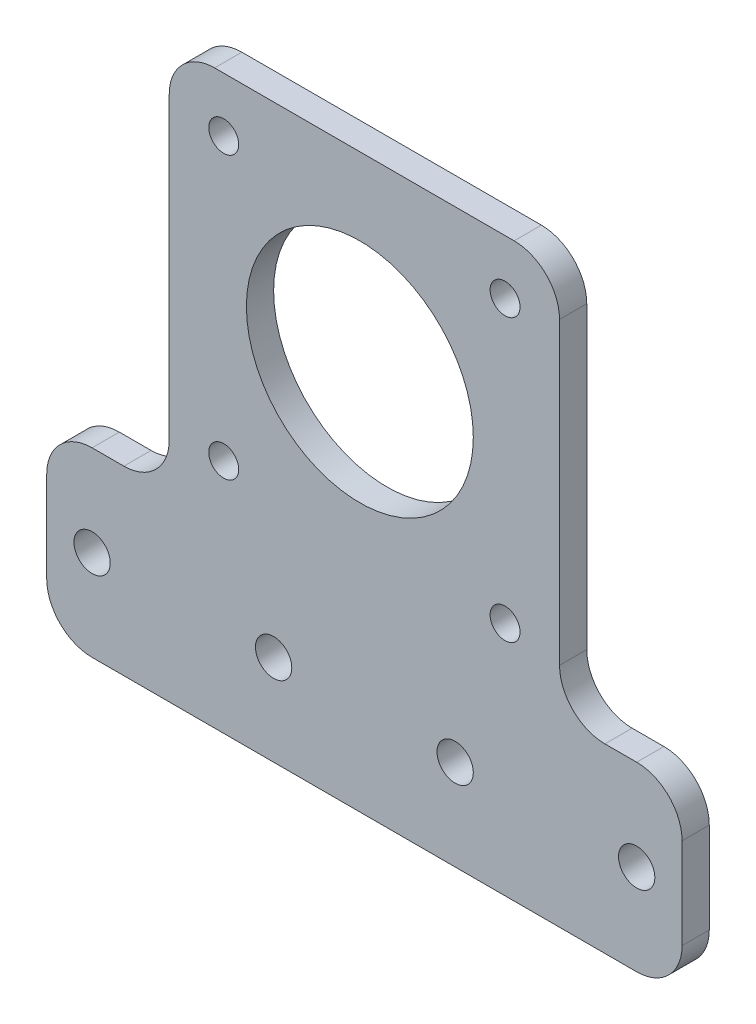
SolidWorks part; units mm, degrees
material "Balsa"
ref_plane "前视基准面" through (0, 0, 0) normal (0, 0, 1) x (1, 0, 0)
ref_plane "上视基准面" through (0, 0, 0) normal (0, 1, 0) x (1, 0, 0)
ref_plane "右视基准面" through (0, 0, 0) normal (1, 0, 0) x (0, 0, -1)
other "Configuration Table"
sketch "Sketch1" plane through (0, 0, 0) normal (0, 0, 1) x (1, 0, 0)
  line L0 (35, 20) -> (35, 49.9488) construction
  line L1 (0, 0) -> (70, 0)
  line L2 (0, 0) -> (0, 20)
  line L3 (0, 20) -> (70, 20)
  line L4 (70, 0) -> (70, 20)
  line L5 (13.5, 41.5) -> (56.5, 41.5) construction
  line L6 (13.5, 63) -> (56.5, 63)
  line L7 (13.5, 63) -> (13.5, 20)
  line L8 (13.5, 20) -> (56.5, 20)
  line L9 (56.5, 63) -> (56.5, 20)
  circle A0 centre (19.5, 57) radius 1.65
  circle A1 centre (50.5, 57) radius 1.65
  circle A2 centre (50.5, 26) radius 1.65
  circle A3 centre (19.5, 26) radius 1.65
  point P17 (20.8475, 41.5)
  dimension "D9" = 3.3
  dimension "D1" = 20
  dimension "D2" = 70
  dimension "D3" = 43
  dimension "D4" = 21.5
  dimension "D5" = 35
  dimension "D6" = 43
  dimension "D7" = 31
  dimension "D8" = 15.5
extrude "Boss-Extrude1" add sketch "Sketch1" along normal blind 3 contours L9 L6 L7 L3 A1 A0 A2 A3 | L1 L4 L3 L2
fillet "Fillet1" radius 5 8 edges at (56.5, 20, 1.5) (70, 20, 1.5) (70, 0, 1.5) (0, 0, 1.5) (0, 20, 1.5) (13.5, 20, 1.5) (13.5, 63, 1.5) (56.5, 63, 1.5)
sketch "Sketch2" plane through (0, 0, 3) normal (0, 0, 1) x (1, 0, 0)
  line L0 (5, 20) -> (8.5, 20) construction
  line L1 (0, 5) -> (0, 15) construction
  circle A0 centre (5, 10) radius 2
  circle A1 centre (25, 10) radius 2
  circle A2 centre (45, 10) radius 2
  circle A3 centre (65, 10) radius 2
  point P6 (24.8551, 10)
  dimension "D2" = 4
  dimension "D5" = 20
  dimension "D1" = 10
  dimension "D3" = 5
  dimension "D4" = 4
extrude "Cut-Extrude1" cut sketch "Sketch2" against normal blind 3
sketch "Sketch3" plane through (0, 0, 3) normal (0, 0, 1) x (1, 0, 0)
  circle A0 centre (34.5, 42) radius 12.5
  circle A1 centre (19.5, 57) radius 1.65 construction
  dimension "D3" = 25
  dimension "D1" = 15
  dimension "D2" = 15
extrude "Cut-Extrude2" cut sketch "Sketch3" against normal blind 3
